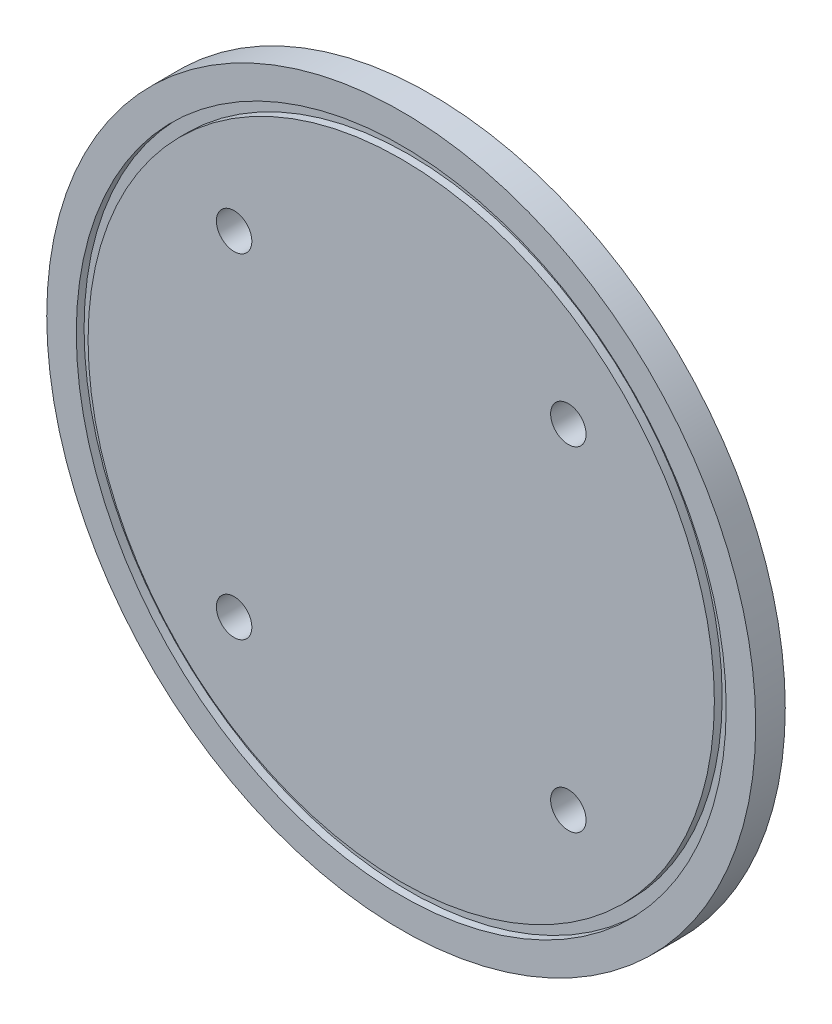
SolidWorks part; units mm, degrees
material "Malleable Cast Iron"
ref_plane "Front Plane" through (0, 0, 0) normal (0, 0, 1) x (1, 0, 0)
ref_plane "Top Plane" through (0, 0, 0) normal (0, 1, 0) x (1, 0, 0)
ref_plane "Right Plane" through (0, 0, 0) normal (1, 0, 0) x (0, 0, -1)
sketch "Sketch1" plane through (0, 0, 0) normal (0, 0, 1) x (1, 0, 0)
  circle A0 centre (0, 0) radius 75
  dimension "D1" = 150
extrude "Boss-Extrude1" add sketch "Sketch1" along normal blind 5
sketch "Sketch2" plane through (0, 0, 5) normal (0, 0, 1) x (1, 0, 0)
  line L0 (0, 0) -> (28.2843, 28.2843) construction
  line L1 (0, 0) -> (38.8683, 0) construction
  circle A0 centre (28.2843, 28.2843) radius 3
  dimension "D1" = 6
  dimension "D2" = 45
  dimension "D3" = 40
extrude "Cut-Extrude1" cut sketch "Sketch2" against normal blind 5
pattern_circular "CirPattern1" count 4 over 360 about axis through (0, 0, 0) along (0, 0, 1) of "Cut-Extrude1"
sketch "Sketch4" plane through (0, 0, 5) normal (0, 0, 1) x (1, 0, 0)
  circle A0 centre (0, 0) radius 53
  circle A1 centre (0, 0) radius 55
  dimension "D1" = 106
  dimension "D2" = 110
extrude "Cut-Extrude3" cut sketch "Sketch4" against normal blind 1.3208
sketch "Sketch5" plane through (0, 0, 5) normal (0, 0, 1) x (1, 0, 0)
  line L6 (0, 0) -> (0, 30.7756) construction
  circle A0 centre (0, 0) radius 60
  circle A2 centre (0, 0) radius 75
  point P29 (0, 0)
  dimension "D1" = 120
  dimension "D7" = 150
extrude "Cut-Extrude4" cut sketch "Sketch5" against normal blind 5
